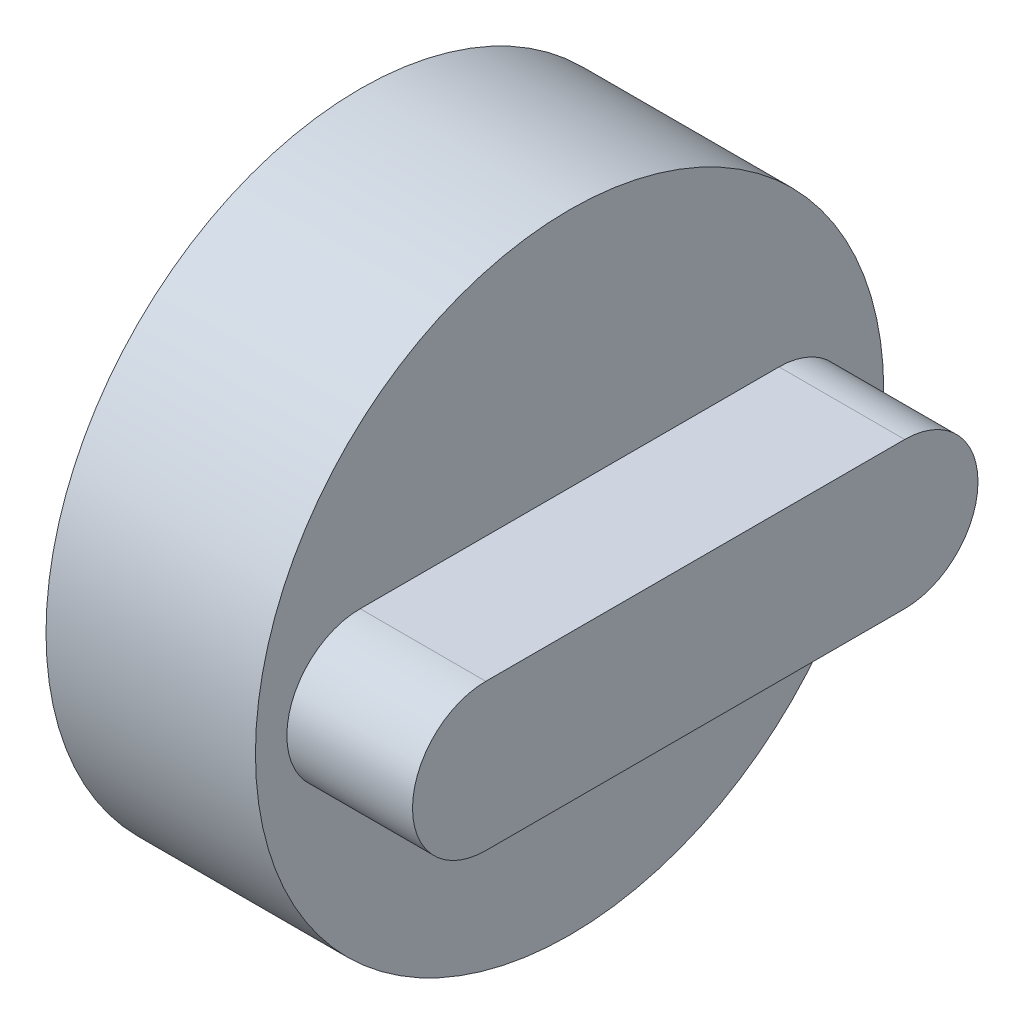
SolidWorks part; units mm, degrees
ref_plane "Front Plane" through (0, 0, 0) normal (0, 0, 1) x (1, 0, 0)
ref_plane "Top Plane" through (0, 0, 0) normal (0, 1, 0) x (1, 0, 0)
ref_plane "Right Plane" through (0, 0, 0) normal (1, 0, 0) x (0, 0, -1)
sketch "Sketch2" plane through (0, 0, 0) normal (1, 0, 0) x (0, 0, -1)
  circle A0 centre (0, 0) radius 15
extrude "Boss-Extrude1" add sketch "Sketch2" along normal blind 10
sketch "Sketch3" plane through (10, 0, 0) normal (1, 0, 0) x (0, 0, -1)
  line L0 (-10, 0) -> (10, 0) construction
  line L1 (-10, 3.5) -> (10, 3.5)
  line L2 (-10, -3.5) -> (10, -3.5)
  arc A0 (-10, 3.5) -> (-10, -3.5) centre (-10, 0) ccw
  arc A1 (10, -3.5) -> (10, 3.5) centre (10, 0) ccw
  point P3 (0, 0)
  dimension "D1" = 0
extrude "Boss-Extrude2" add sketch "Sketch3" along normal blind 6
sketch "Sketch4" plane through (0, 0, 0) normal (-1, 0, 0) x (0, 0, 1)
  circle A0 centre (0, 0) radius 2.5
extrude "Cut-Extrude1" cut sketch "Sketch4" against normal blind 8
sketch "Sketch5" plane through (8, 0, 0) normal (-1, 0, 0) x (0, 0, 1)
  line L1 (-0.4388, 2.452) -> (0.3872, 2.452)
  line L2 (-0.4388, 2.452) -> (-0.4388, -2.5553)
  line L3 (-0.4388, -2.5553) -> (0.3872, -2.5553)
  line L4 (0.3872, 2.452) -> (0.3872, -2.5553) construction
sketch "Sketch6" plane through (8, 0, 0) normal (-1, 0, 0) x (0, 0, 1)
  line L1 (-0.4388, 2.452) -> (0.3872, 2.452)
  line L2 (-0.4388, 2.452) -> (-0.4388, -2.5553)
  line L3 (-0.4388, -2.5553) -> (0.3872, -2.5553)
  line L4 (0.3872, 2.452) -> (0.3872, -2.5553)
extrude "Boss-Extrude3" add sketch "Sketch6" along normal blind 15
